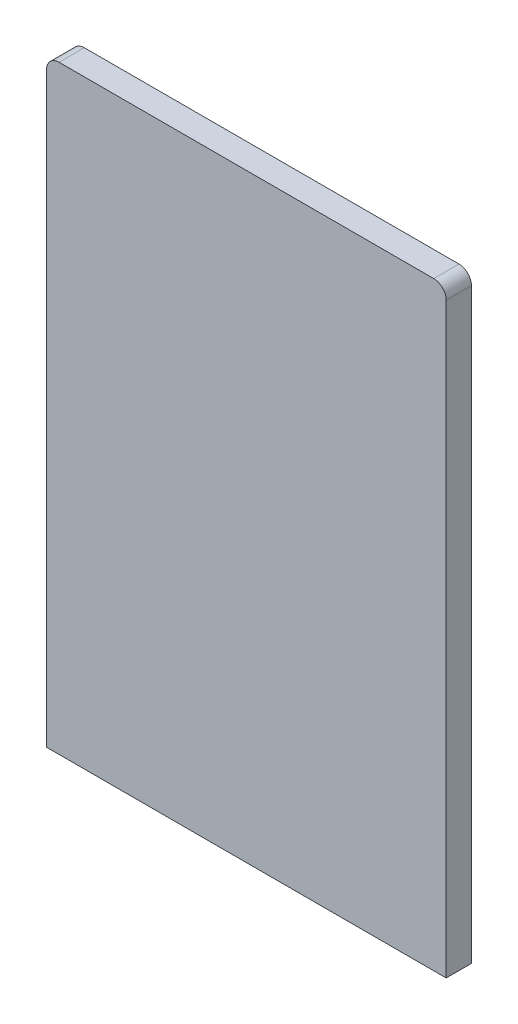
SolidWorks part; units mm, degrees
ref_plane "Front Plane" through (0, 0, 0) normal (0, 0, 1) x (1, 0, 0)
ref_plane "Top Plane" through (0, 0, 0) normal (0, 1, 0) x (1, 0, 0)
ref_plane "Right Plane" through (0, 0, 0) normal (1, 0, 0) x (0, 0, -1)
sketch "Sketch1" plane through (0, 0, 0) normal (0, 0, 1) x (1, 0, 0)
  line L0 (-2.75, -2.75) -> (-2.75, -8)
  line L1 (-2.75, -2.75) -> (2.75, -2.75)
  line L2 (-2.75, -2.75) -> (-2.75, 2.75)
  line L3 (-2.75, 2.75) -> (2.75, 2.75)
  line L4 (2.75, -2.75) -> (2.75, 2.75)
  line L5 (-2.75, -2.75) -> (2.75, 2.75) construction
  line L6 (-2.75, 2.75) -> (2.75, -2.75) construction
  line L7 (-4, -4) -> (4, -4)
  line L8 (-4, -4) -> (-4, 4)
  line L9 (-4, 4) -> (4, 4)
  line L10 (4, -4) -> (4, 4)
  line L11 (-4, -4) -> (4, 4) construction
  line L12 (-4, 4) -> (4, -4) construction
  line L13 (-4, -4) -> (4, -4)
  line L14 (-4, -4) -> (-4, -8)
  line L15 (-4, -8) -> (4, -8)
  line L16 (4, -4) -> (4, -8)
  line L17 (2.75, -2.75) -> (2.75, -8)
  point P0 (0, 0)
  point P5 (0, 0)
  dimension "D1" = 5.5
  dimension "D2" = 8
  dimension "D3" = 4
  dimension "D4" = 8
extrude "Boss-Extrude1" add sketch "Sketch1" along normal blind 0.105 contours L13 L17 L15 L16 | L4 L17 L13 L10 L9 L8 L7 L0 L2 L3 | L14 L15 L0 L7
fillet "Fillet1" radius 0.25 4 edges at (-4, 4, 0.0525) (4, 4, 0.0525) (-2.75, 2.75, 0.0525) (2.75, 2.75, 0.0525)
sketch "Sketch2" plane through (0, 0, 0) normal (0, 0, -1) x (-1, 0, 0)
  line L0 (-2.75, -8) -> (2.75, -8)
  line L8 (4, -8) -> (4, 3.75)
  line L9 (3.75, 4) -> (-3.75, 4)
  line L10 (-4, 3.75) -> (-4, -8)
  line L11 (-4, -8) -> (-2.75, -8)
  line L12 (-2.75, -8) -> (-2.75, 2.5)
  line L13 (-2.5, 2.75) -> (2.5, 2.75)
  line L14 (2.75, 2.5) -> (2.75, -8)
  line L15 (2.75, -8) -> (4, -8)
  line L16 (4, -8) -> (4, 3.75)
  line L17 (3.75, 4) -> (-3.75, 4)
  line L18 (-4, 3.75) -> (-4, -8)
  line L19 (-4, -8) -> (-2.75, -8)
  line L20 (-2.75, -8) -> (-2.75, 2.5)
  line L21 (-2.5, 2.75) -> (2.5, 2.75)
  line L22 (2.75, 2.5) -> (2.75, -8)
  line L23 (2.75, -8) -> (4, -8)
  arc A4 (4, 3.75) -> (3.75, 4) centre (3.75, 3.75) ccw
  arc A5 (-3.75, 4) -> (-4, 3.75) centre (-3.75, 3.75) ccw
  arc A6 (-2.5, 2.75) -> (-2.75, 2.5) centre (-2.5, 2.5) ccw
  arc A7 (2.75, 2.5) -> (2.5, 2.75) centre (2.5, 2.5) ccw
  arc A8 (4, 3.75) -> (3.75, 4) centre (3.75, 3.75) ccw
  arc A9 (-3.75, 4) -> (-4, 3.75) centre (-3.75, 3.75) ccw
  arc A10 (-2.5, 2.75) -> (-2.75, 2.5) centre (-2.5, 2.5) ccw
  arc A11 (2.75, 2.5) -> (2.5, 2.75) centre (2.5, 2.5) ccw
  line M13 (4, -8) -> (4, 3.75)
  arc M14 (4, 3.75) -> (3.75, 4) centre (3.75, 3.75) ccw
  line M15 (3.75, 4) -> (-3.75, 4)
  arc M16 (-3.75, 4) -> (-4, 3.75) centre (-3.75, 3.75) ccw
  line M17 (-4, 3.75) -> (-4, -8)
  line M18 (-4, -8) -> (-2.75, -8)
  line M19 (-2.75, -8) -> (-2.75, 2.5)
  arc M20 (-2.75, 2.5) -> (-2.5, 2.75) centre (-2.5, 2.5) cw
  line M21 (-2.5, 2.75) -> (2.5, 2.75)
  arc M22 (2.5, 2.75) -> (2.75, 2.5) centre (2.5, 2.5) cw
  line M23 (2.75, 2.5) -> (2.75, -8)
  line M24 (2.75, -8) -> (4, -8)
  dimension "D1" = 0
extrude "Boss-Extrude2" add sketch "Sketch2" along normal blind 0.2 contours M24 M13 M14 M15 M16 M17 M18 M19 M20 M21 M22 M23 | L0 M19 M23 M22 M21 M20
sketch "Sketch4" plane through (0, 0, 0.105) normal (0, 0, 1) x (1, 0, 0)
  line L0 (-2.75, -8) -> (2.75, -8)
  line L8 (3.75, 4) -> (-3.75, 4)
  line L9 (-4, 3.75) -> (-4, -8)
  line L10 (-4, -8) -> (-2.75, -8)
  line L11 (-2.75, -8) -> (-2.75, 2.5)
  line L12 (-2.5, 2.75) -> (2.5, 2.75)
  line L13 (2.75, 2.5) -> (2.75, -8)
  line L14 (2.75, -8) -> (4, -8)
  line L15 (4, -8) -> (4, 3.75)
  line L16 (3.75, 4) -> (-3.75, 4)
  line L17 (-4, 3.75) -> (-4, -8)
  line L18 (-4, -8) -> (-2.75, -8)
  line L19 (-2.75, -8) -> (-2.75, 2.5)
  line L20 (-2.5, 2.75) -> (2.5, 2.75)
  line L21 (2.75, 2.5) -> (2.75, -8)
  line L22 (2.75, -8) -> (4, -8)
  line L23 (4, -8) -> (4, 3.75)
  arc A4 (-3.75, 4) -> (-4, 3.75) centre (-3.75, 3.75) ccw
  arc A5 (-2.5, 2.75) -> (-2.75, 2.5) centre (-2.5, 2.5) ccw
  arc A6 (2.75, 2.5) -> (2.5, 2.75) centre (2.5, 2.5) ccw
  arc A7 (4, 3.75) -> (3.75, 4) centre (3.75, 3.75) ccw
  arc A8 (-3.75, 4) -> (-4, 3.75) centre (-3.75, 3.75) ccw
  arc A9 (-2.5, 2.75) -> (-2.75, 2.5) centre (-2.5, 2.5) ccw
  arc A10 (2.75, 2.5) -> (2.5, 2.75) centre (2.5, 2.5) ccw
  arc A11 (4, 3.75) -> (3.75, 4) centre (3.75, 3.75) ccw
  line M13 (3.75, 4) -> (-3.75, 4)
  arc M14 (-3.75, 4) -> (-4, 3.75) centre (-3.75, 3.75) ccw
  line M15 (-4, 3.75) -> (-4, -8)
  line M16 (-4, -8) -> (-2.75, -8)
  line M17 (-2.75, -8) -> (-2.75, 2.5)
  arc M18 (-2.75, 2.5) -> (-2.5, 2.75) centre (-2.5, 2.5) cw
  line M19 (-2.5, 2.75) -> (2.5, 2.75)
  arc M20 (2.5, 2.75) -> (2.75, 2.5) centre (2.5, 2.5) cw
  line M21 (2.75, 2.5) -> (2.75, -8)
  line M22 (2.75, -8) -> (4, -8)
  line M23 (4, -8) -> (4, 3.75)
  arc M24 (4, 3.75) -> (3.75, 4) centre (3.75, 3.75) ccw
  dimension "D1" = 0
extrude "Boss-Extrude3" add sketch "Sketch4" along normal blind 0.2 contours M24 M13 M14 M15 M16 M17 M18 M19 M20 M21 M22 M23 | L0 M17 M21 M20 M19 M18
